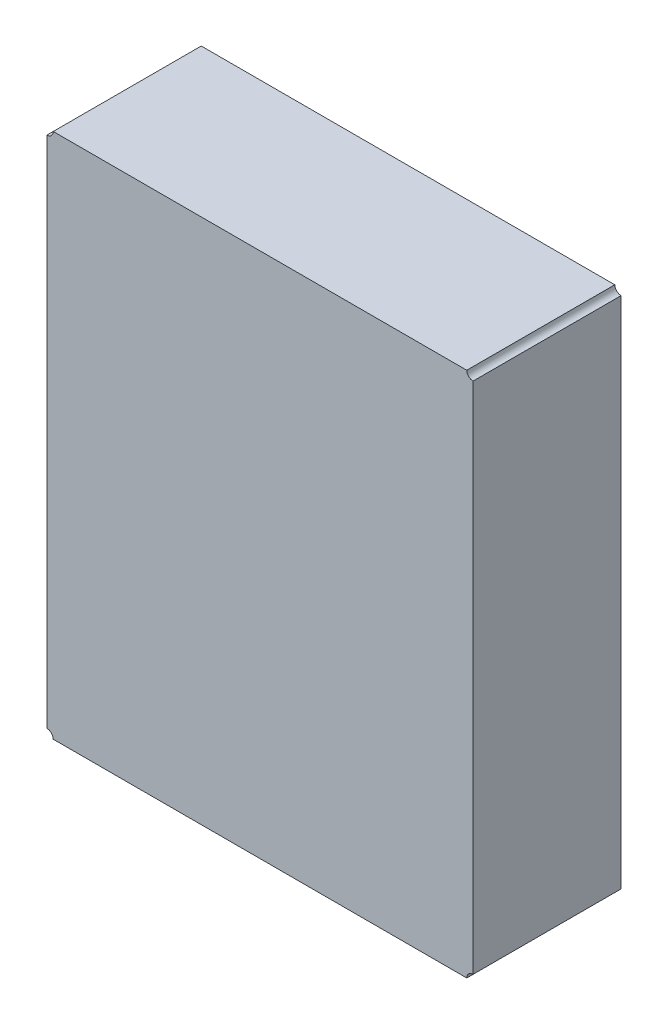
SolidWorks part; units mm, degrees
ref_plane "前视基准面" through (0, 0, 0) normal (0, 0, 1) x (1, 0, 0)
ref_plane "上视基准面" through (0, 0, 0) normal (0, 1, 0) x (1, 0, 0)
ref_plane "右视基准面" through (0, 0, 0) normal (1, 0, 0) x (0, 0, -1)
sketch "草图1" plane through (0, 0, 0) normal (0, 0, 1) x (1, 0, 0)
  line L0 (90.932, 75.946) -> (90.932, 81.28)
  line L1 (90.932, 75.946) -> (95.25, 75.946)
  line L2 (95.25, 75.946) -> (95.25, 81.28)
  line L3 (90.932, 81.28) -> (95.25, 81.28)
  circle A0 centre (90.932, 75.946) radius 0.0635
  circle A1 centre (90.932, 81.28) radius 0.0635
  circle A2 centre (90.932, 75.946) radius 0.0635
  circle A3 centre (95.25, 75.946) radius 0.0635
  circle A4 centre (95.25, 75.946) radius 0.0635
  circle A5 centre (95.25, 81.28) radius 0.0635
  circle A6 centre (90.932, 81.28) radius 0.0635
  circle A7 centre (95.25, 81.28) radius 0.0635
extrude "凸台-拉伸1" add sketch "草图1" along normal blind 1.5 contours A5 L3 A1 L0 A0 L1 A3 L2
